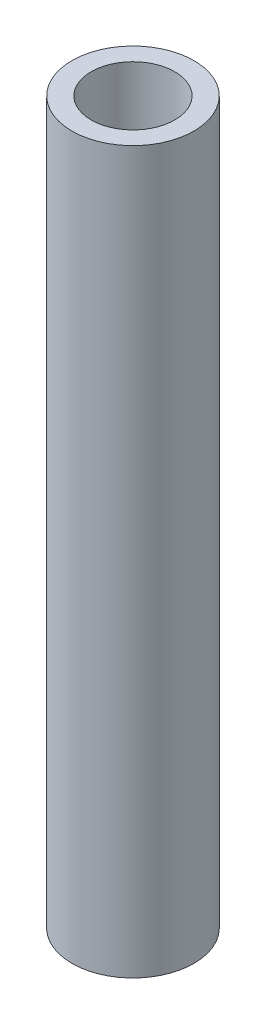
SolidWorks part; units mm, degrees
ref_plane "Front Plane" through (0, 0, 0) normal (0, 0, 1) x (1, 0, 0)
ref_plane "Top Plane" through (0, 0, 0) normal (0, 1, 0) x (1, 0, 0)
ref_plane "Right Plane" through (0, 0, 0) normal (1, 0, 0) x (0, 0, -1)
sketch "Sketch1" plane through (0, 0, 0) normal (0, 1, 0) x (1, 0, 0)
  circle A0 centre (0, 0) radius 12.7
  circle A1 centre (0, 0) radius 8.7
  dimension "D1" = 25.4
  dimension "D2" = 17.4
extrude "Boss-Extrude1" add sketch "Sketch1" along normal blind 150
sketch "Sketch3" plane through (0, 0, 0) normal (0, 0, 1) x (1, 0, 0)
  circle A0 centre (0, 415) radius 2.5 construction
  circle A1 centre (0, 415) radius 2.5
  arc A2 (0, 266.255) -> (0, 271.255) centre (0, 268.755) ccw construction
  arc A3 (0, 271.255) -> (0, 266.255) centre (0, 268.755) ccw construction
  arc A4 (0, 266.255) -> (0, 271.255) centre (0, 268.755) ccw
  arc A5 (0, 271.255) -> (0, 266.255) centre (0, 268.755) ccw
extrude "Cut-Extrude1" [suppressed] cut sketch "Sketch3" against normal through all both and the other way through all
sketch "Sketch4" plane through (0, 0, 0) normal (1, 0, 0) x (0, 0, -1)
  circle A0 centre (0, 253.755) radius 2.5 construction
  circle A1 centre (0, 283.755) radius 2.5 construction
  circle A2 centre (0, 253.755) radius 2.5
  circle A3 centre (0, 283.755) radius 2.5
extrude "Cut-Extrude2" [suppressed] cut sketch "Sketch4" against normal through all both and the other way through all
sketch "Sketch6" plane through (0, 0, 0) normal (0, 1, 0) x (1, 0, 0)
  circle A0 centre (0, 0) radius 12.7 construction
  circle A1 centre (0, 0) radius 12.7
extrude "Cut-Extrude4" [suppressed] cut sketch "Sketch6" along normal blind 161.65
